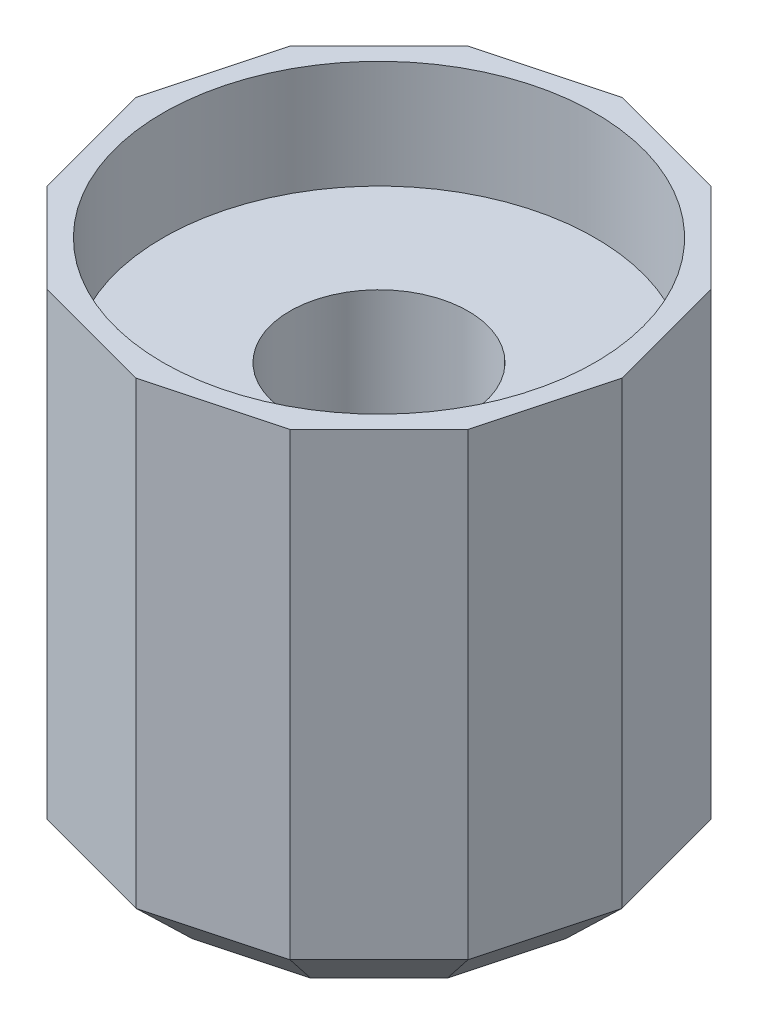
SolidWorks part; units mm, degrees
ref_plane "Front Plane" through (0, 0, 0) normal (0, 0, 1) x (1, 0, 0)
ref_plane "Top Plane" through (0, 0, 0) normal (0, 1, 0) x (1, 0, 0)
ref_plane "Right Plane" through (0, 0, 0) normal (1, 0, 0) x (0, 0, -1)
sketch "Sketch1" plane through (0, 0, 0) normal (0, 1, 0) x (1, 0, 0)
  line L1 (0, 9) -> (-4.5, 7.7942)
  line L2 (-4.5, 7.7942) -> (-7.7942, 4.5)
  line L3 (-7.7942, 4.5) -> (-9, 0)
  line L4 (-9, 0) -> (-7.7942, -4.5)
  line L5 (-7.7942, -4.5) -> (-4.5, -7.7942)
  line L6 (-4.5, -7.7942) -> (0, -9)
  line L7 (0, -9) -> (4.5, -7.7942)
  line L8 (4.5, -7.7942) -> (7.7942, -4.5)
  line L9 (7.7942, -4.5) -> (9, 0)
  line L10 (9, 0) -> (7.7942, 4.5)
  line L11 (7.7942, 4.5) -> (4.5, 7.7942)
  line L12 (4.5, 7.7942) -> (0, 9)
  circle A1 centre (0, 0) radius 8.6933 construction
extrude "Boss-Extrude1" add sketch "Sketch1" along normal blind 19
sketch "Sketch2" plane through (0, 19, 0) normal (0, 1, 0) x (1, 0, 0)
  circle A0 centre (0, 0) radius 8
extrude "Cut-Extrude1" cut sketch "Sketch2" against normal blind 4
sketch "Sketch3" plane through (0, 15, 0) normal (0, 1, 0) x (1, 0, 0)
  circle A0 centre (0, 0) radius 3.3
extrude "Cut-Extrude2" cut sketch "Sketch3" against normal blind 14
chamfer "Chamfer1" distance 2 angle 45 12 edges at (-6.1471, 0, 6.1471) (-2.25, 0, 8.3971) (2.25, 0, 8.3971) (6.1471, 0, 6.1471) (8.3971, 0, 2.25) (8.3971, 0, -2.25) (6.1471, 0, -6.1471) (2.25, 0, -8.3971) (-2.25, 0, -8.3971) (-6.1471, 0, -6.1471) (-8.3971, 0, -2.25) (-8.3971, 0, 2.25)
